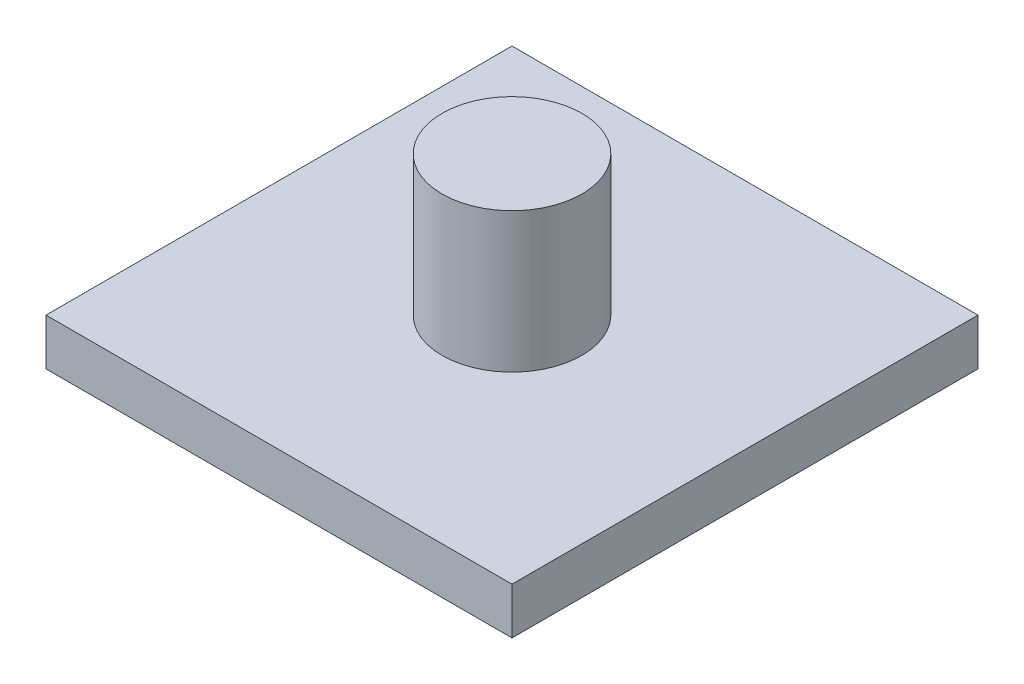
SolidWorks part; units mm, degrees
ref_plane "Front Plane" through (0, 0, 0) normal (0, 0, 1) x (1, 0, 0)
ref_plane "Top Plane" through (0, 0, 0) normal (0, 1, 0) x (1, 0, 0)
ref_plane "Right Plane" through (0, 0, 0) normal (1, 0, 0) x (0, 0, -1)
sketch "Sketch1" plane through (0, 0, 0) normal (0, 1, 0) x (1, 0, 0)
  line L1 (0, 0) -> (20, 0)
  line L2 (0, 0) -> (0, 20)
  line L3 (0, 20) -> (20, 20)
  line L4 (20, 0) -> (20, 20)
  dimension "D1" = 20
  dimension "D2" = 20
extrude "Boss-Extrude1" add sketch "Sketch1" along normal blind 2
sketch "Sketch2" plane through (0, 2, 0) normal (0, 1, 0) x (1, 0, 0)
  line L0 (0, 20) -> (20, 0)
  circle A0 centre (10, 10) radius 3
  dimension "D1" = 6
extrude "Boss-Extrude2" add sketch "Sketch2" along normal blind 6 contours A0
